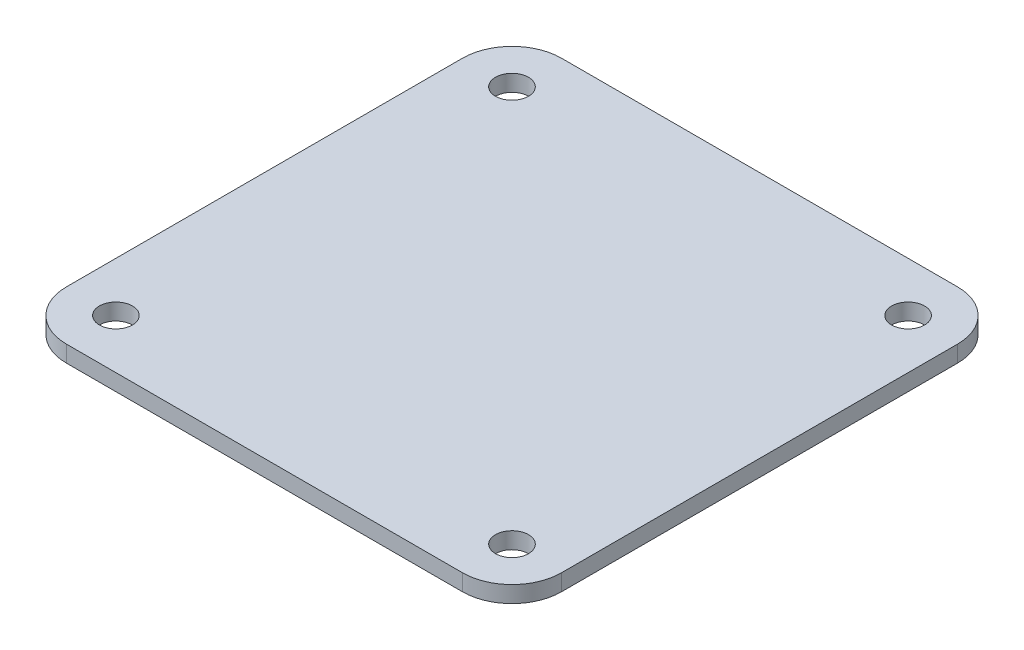
SolidWorks part; units mm, degrees
ref_plane "Front Plane" through (0, 0, 0) normal (0, 0, 1) x (1, 0, 0)
ref_plane "Top Plane" through (0, 0, 0) normal (0, 1, 0) x (1, 0, 0)
ref_plane "Right Plane" through (0, 0, 0) normal (1, 0, 0) x (0, 0, -1)
sketch "Sketch1" plane through (0, 0, 0) normal (0, 1, 0) x (1, 0, 0)
  line L1 (-19.05, -19.05) -> (19.05, -19.05) construction
  line L2 (-19.05, -19.05) -> (-19.05, 19.05) construction
  line L3 (-19.05, 19.05) -> (19.05, 19.05) construction
  line L4 (19.05, -19.05) -> (19.05, 19.05) construction
  line L5 (-19.05, -19.05) -> (19.05, 19.05) construction
  line L6 (-19.05, 19.05) -> (19.05, -19.05) construction
  line L7 (23.8125, -23.8125) -> (-23.8125, -23.8125)
  line L8 (23.8125, -23.8125) -> (23.8125, 23.8125)
  line L9 (23.8125, 23.8125) -> (-23.8125, 23.8125)
  line L10 (-23.8125, -23.8125) -> (-23.8125, 23.8125)
  line L11 (23.8125, -23.8125) -> (-23.8125, 23.8125) construction
  line L12 (23.8125, 23.8125) -> (-23.8125, -23.8125) construction
  circle A0 centre (-19.05, 19.05) radius 1.5875
  circle A1 centre (19.05, 19.05) radius 1.5875
  circle A2 centre (19.05, -19.05) radius 1.5875
  circle A3 centre (-19.05, -19.05) radius 1.5875
  point P0 (0, 0)
  point P10 (0, 0)
  dimension "D1" = 3.175
  dimension "D2" = 38.1
  dimension "D3" = 4.7625
extrude "Boss-Extrude1" add sketch "Sketch1" along normal blind 1.5875
fillet "Fillet1" radius 4.7625 4 edges at (-23.8125, 0.7937, -23.8125) (23.8125, 0.7937, -23.8125) (23.8125, 0.7937, 23.8125) (-23.8125, 0.7937, 23.8125)
